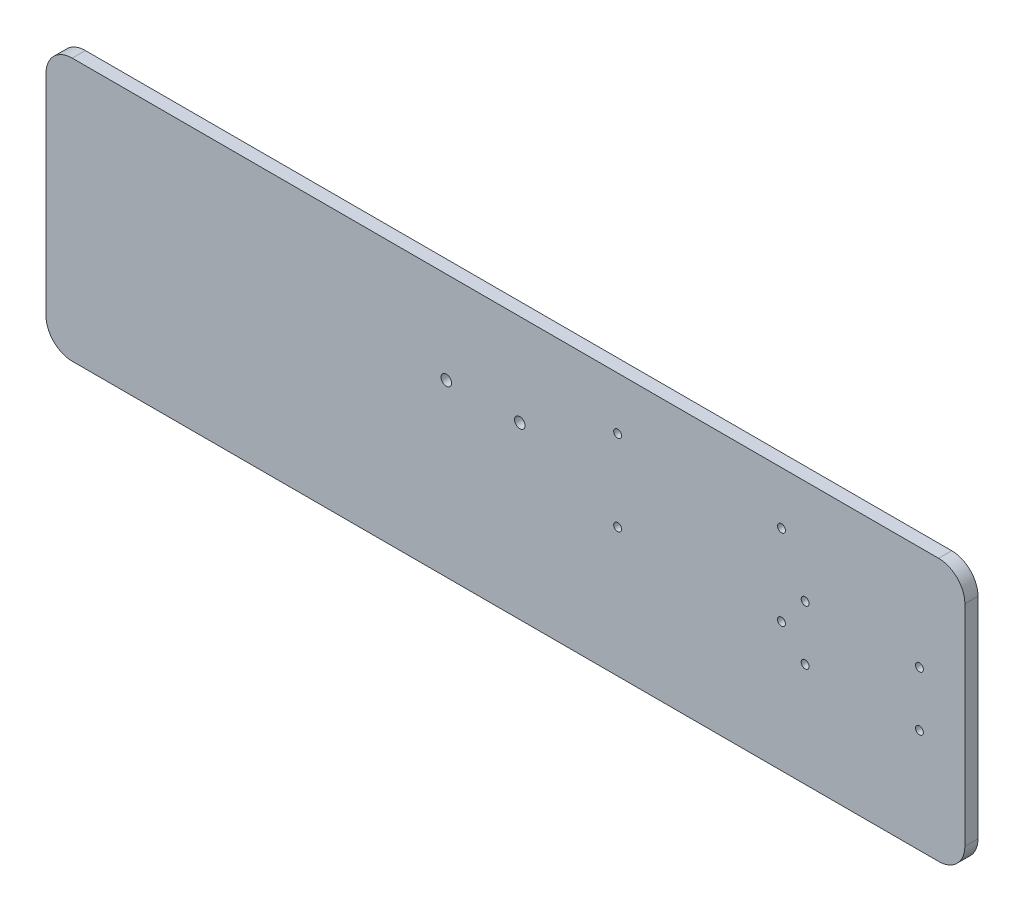
SolidWorks part; units mm, degrees
ref_plane "Front Plane" through (0, 0, 0) normal (0, 0, 1) x (1, 0, 0)
ref_plane "Top Plane" through (0, 0, 0) normal (0, 1, 0) x (1, 0, 0)
ref_plane "Right Plane" through (0, 0, 0) normal (1, 0, 0) x (0, 0, -1)
sketch "Sketch1" plane through (0, 0, 0) normal (0, 0, 1) x (1, 0, 0)
  line L1 (-165, -50) -> (165, -50)
  line L2 (-175, -40) -> (-175, 40)
  line L3 (-165, 50) -> (165, 50)
  line L4 (175, -40) -> (175, 40)
  line L5 (-175, -50) -> (175, 50) construction
  line L6 (-175, 50) -> (175, -50) construction
  arc A0 (165, -50) -> (175, -40) centre (165, -40) ccw
  arc A1 (-175, 40) -> (-165, 50) centre (-165, 40) cw
  arc A2 (-165, -50) -> (-175, -40) centre (-165, -40) cw
  arc A3 (165, 50) -> (175, 40) centre (165, 40) cw
  point P0 (0, 0)
  dimension "D3" = 10
  dimension "D1" = 350
  dimension "D2" = 100
extrude "Boss-Extrude1" add sketch "Sketch1" along normal blind 5
sketch "Sketch2" plane through (0, 0, 0) normal (0, 0, -1) x (-1, 0, 0)
  line L0 (-165, 50) -> (165, 50) construction
  line L5 (-5.4571, 15) -> (39.4754, 15) construction
  line L7 (-105.1538, -0.8145) -> (-42.7384, -0.8145) construction
  line L8 (-105.1538, -0.8145) -> (-105.1538, 30) construction
  line L9 (-105.1538, 30) -> (-42.7384, 30) construction
  line L10 (-42.7384, -0.8145) -> (-42.7384, 30) construction
  line L11 (-105.1538, -0.8145) -> (-42.7384, 30) construction
  line L12 (-105.1538, 30) -> (-42.7384, -0.8145) construction
  circle A0 centre (-5.4571, 15) radius 2
  circle A1 centre (22.5281, 15) radius 2
  circle A6 centre (-105.1538, 30) radius 1.5
  circle A7 centre (-42.7384, 30) radius 1.5
  circle A8 centre (-42.7384, -0.8145) radius 1.5
  circle A9 centre (-105.1538, -0.8145) radius 1.5
  circle A10 centre (-114.15, -10.395) radius 1.5 construction
  circle A11 centre (-114.15, 10.395) radius 1.5 construction
  circle A12 centre (-157.7, -10.395) radius 1.5 construction
  circle A13 centre (-157.7, 10.395) radius 1.5 construction
  circle A14 centre (-114.15, -10.395) radius 1.5
  circle A15 centre (-114.15, 10.395) radius 1.5
  circle A16 centre (-157.7, -10.395) radius 1.5
  circle A17 centre (-157.7, 10.395) radius 1.5
  point P5 (-73.9461, 14.5928)
  point P27 (0, 0)
  dimension "D1" = 3
  dimension "D3" = 35
  dimension "D4" = 4
  dimension "D2" = 20
extrude "Cut-Extrude1" cut sketch "Sketch2" against normal up to next
